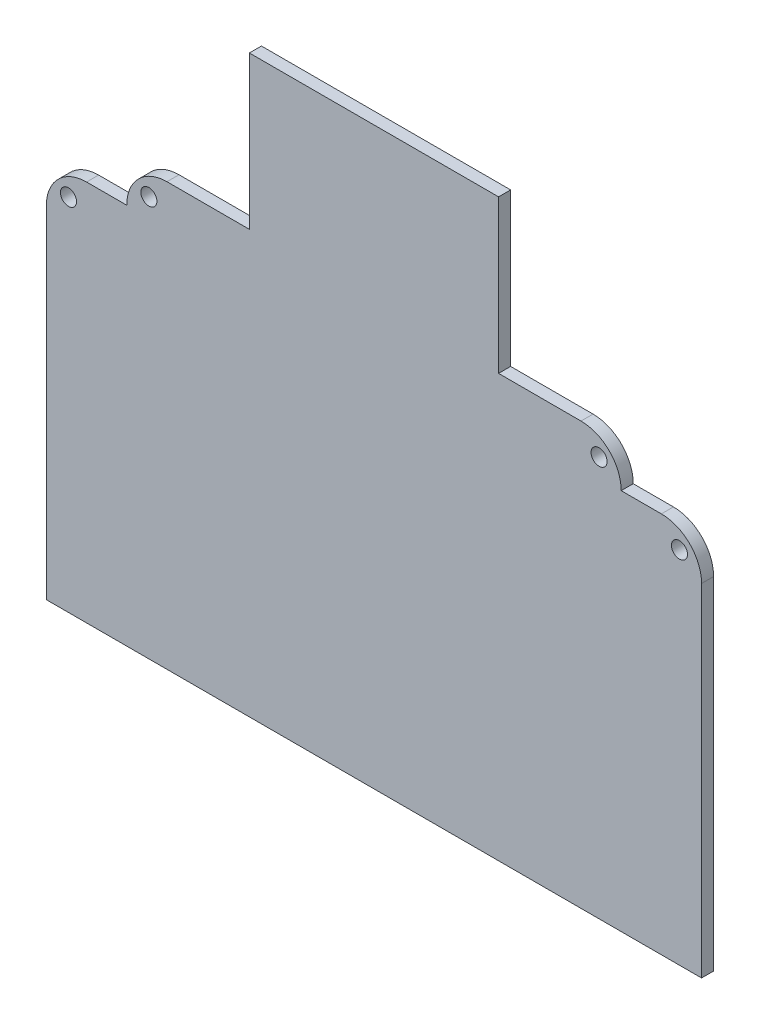
SolidWorks part; units mm, degrees
ref_plane "Plan de face" through (0, 0, 0) normal (0, 0, 1) x (1, 0, 0)
ref_plane "Plan de dessus" through (0, 0, 0) normal (0, 1, 0) x (1, 0, 0)
ref_plane "Plan de droite" through (0, 0, 0) normal (1, 0, 0) x (0, 0, -1)
sketch "Esquisse2" plane through (0, 0, 0) normal (0, 0, 1) x (1, 0, 0)
  line L0 (-57.997, -5.0091) -> (105.003, -5.0091)
  line L1 (105.003, -5.0091) -> (105.003, -0.0091)
  line L2 (95.003, 9.9909) -> (85.003, 9.9909)
  line L3 (-27.9952, 20.0587) -> (75.009, 19.9969)
  line L4 (-27.9952, 20.0587) -> (-27.997, 20.0587)
  line L5 (85.003, 9.9969) -> (85.003, 9.9909)
  line L6 (-37.997, 9.9909) -> (-47.997, 9.9909)
  line L7 (-57.997, -0.0091) -> (-57.997, -5.0091)
  line L8 (-37.997, 10.0587) -> (-37.997, 9.9909)
  arc A0 (105.003, -0.0091) -> (95.003, 9.9909) centre (95.003, -0.0091) ccw
  arc A1 (-47.997, 9.9909) -> (-57.997, -0.0091) centre (-47.997, -0.0091) ccw
  arc A2 (-27.997, 20.0587) -> (-37.997, 10.0587) centre (-27.997, 10.0587) ccw
  arc A3 (75.009, 19.9969) -> (85.003, 9.9969) centre (75.003, 9.9969) cw
  point P10 (105.003, 9.9909)
  point P13 (-57.997, 9.9909)
  point P18 (85.003, 19.9909)
  dimension "D6" = 10
  dimension "D7" = 10
  dimension "D2" = 10
  dimension "D3" = 10
  dimension "D1" = 15
  dimension "D4" = 163
  dimension "D5" = 20
  dimension "D8" = 15
  dimension "D9" = 10
  dimension "D10" = 123
extrude "Boss.-Extru.1" add sketch "Esquisse2" along normal blind 3
sketch "Esquisse4" plane through (0, 0, 3) normal (0, 0, 1) x (1, 0, 0)
  line L0 (-57.997, -0.0091) -> (-57.997, -5.0091) construction
  line L1 (-37.997, 9.9909) -> (-47.997, 9.9909) construction
  line L2 (95.003, 9.9909) -> (85.003, 9.9909) construction
  line L3 (105.003, -5.0091) -> (105.003, -0.0091) construction
  line L4 (75.009, 19.9969) -> (-27.9952, 20.0587) construction
  circle A0 centre (-32.497, 14.5587) radius 2
  circle A1 centre (79.503, 14.4942) radius 2
  circle A2 centre (99.503, 4.4909) radius 2
  circle A3 centre (-52.497, 4.4909) radius 2
  dimension "D1" = 4
  dimension "D2" = 4
  dimension "D3" = 4
  dimension "D4" = 4
  dimension "D5" = 5.5
  dimension "D6" = 5.5
  dimension "D7" = 5.5
  dimension "D8" = 5.5
  dimension "D9" = 5.5
  dimension "D10" = 5.5
  dimension "D11" = 5.5
  dimension "D12" = 5.5
extrude "Enlèv. mat.-Extru.1" cut sketch "Esquisse4" against normal blind 10
sketch "Esquisse5" plane through (0, 0, 3) normal (0, 0, 1) x (1, 0, 0)
  line L0 (-7.497, 20.0464) -> (-7.497, 58.0464)
  line L1 (75.009, 19.9969) -> (-27.9952, 20.0587) construction
  line L2 (-7.497, 58.0464) -> (54.503, 58.0464)
  line L3 (54.503, 58.0464) -> (54.503, 20.0092)
  line L4 (-7.497, 20.0464) -> (54.503, 20.0092)
  arc A0 (-27.997, 20.0587) -> (-37.997, 10.0587) centre (-27.997, 10.0587) ccw construction
  arc A1 (85.003, 9.9969) -> (75.009, 19.9969) centre (75.003, 9.9969) ccw construction
  dimension "D1" = 38
  dimension "D2" = 62
  dimension "D3" = 20.5
  dimension "D4" = 20.5
extrude "Boss.-Extru.2" add sketch "Esquisse5" against normal blind 3
sketch "Esquisse6" plane through (0, 0, 3) normal (0, 0, 1) x (1, 0, 0)
  line L0 (-57.997, -5.0091) -> (-57.997, -85.0091)
  line L1 (-57.997, -85.0091) -> (105.003, -85.0091)
  line L2 (105.003, -85.0091) -> (105.003, -5.0091)
  line L3 (-57.997, -5.0091) -> (105.003, -5.0091) construction
  line L4 (105.003, -5.0091) -> (-57.997, -5.0091)
  dimension "D1" = 80
extrude "Boss.-Extru.3" add sketch "Esquisse6" against normal blind 3
